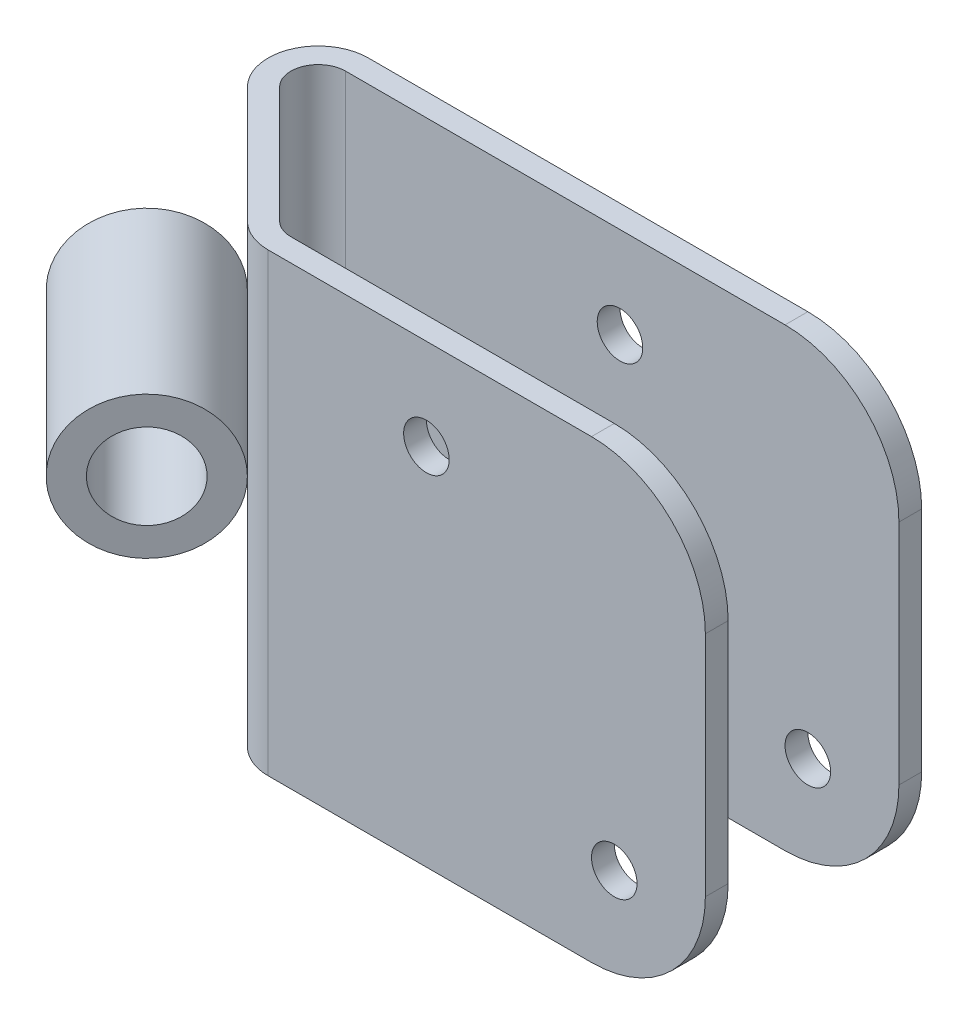
SolidWorks part; units mm, degrees
ref_plane "Front Plane" through (0, 0, 0) normal (0, 0, 1) x (1, 0, 0)
ref_plane "Top Plane" through (0, 0, 0) normal (0, 1, 0) x (1, 0, 0)
ref_plane "Right Plane" through (0, 0, 0) normal (1, 0, 0) x (0, 0, -1)
sketch "Sketch1" plane through (0, 0, 0) normal (0, 1, 0) x (1, 0, 0)
  line L0 (46.2173, -24.4543) -> (48.0056, -0.3907) construction
  line L1 (0, 0) -> (61.722, 0)
  line L2 (-3.9513, -9.5393) -> (9.0027, -22.4933)
  line L3 (12.954, -24.13) -> (61.722, -24.13)
  line L4 (61.722, -24.13) -> (61.722, 0) construction
  line L5 (-3.9513, -1.6367) -> (-7.9026, -5.588) construction
  line L6 (-7.9026, -5.588) -> (-9.6987, -3.7919) construction
  arc A0 (0, 0) -> (-3.9513, -9.5393) centre (0, -5.588) ccw
  arc A1 (9.0027, -22.4933) -> (12.954, -24.13) centre (12.954, -18.542) ccw
  dimension "D3" = 5.588
  dimension "D4" = 5.588
  dimension "D6" = 67.31
  dimension "D1" = 24.13
  dimension "D2" = 45
  dimension "D5" = 24.13
  dimension "D7" = 2.54
extrude "Extrude-Thin1" add sketch "Sketch1" along normal mid plane 50.8 thin
ref_plane "Plane5" through (-9.6987, 0, 3.7919) normal (-0.7071, 0, -0.7071) x (-0.7071, 0, 0.7071)
sketch "Sketch2" plane through (-9.6987, 25.4, 3.7919) normal (0.7071, 0, 0.7071) x (0.7071, 0, -0.7071)
  line L0 (0, 0) -> (0, -50.8) construction
  line L1 (0, 0) -> (0, -50.8) construction
  circle A0 centre (-7.9375, -25.4) radius 7.9375
  circle A1 centre (-7.9375, -25.4) radius 4.7625
  point P4 (-11.1421, -22.5042)
  point P6 (0, 0)
  point P7 (0, -25.4)
  dimension "D1" = 15.875
  dimension "D2" = 9.525
extrude "Boss-Extrude2" add sketch "Sketch2" along normal blind 25.4 separate body
fillet "Fillet1" radius 12.7 4 edges at (61.722, -25.4, 22.86) (61.722, -25.4, 1.27) (61.722, 25.4, 1.27) (61.722, 25.4, 22.86)
sketch "Sketch4" plane through (0, 0, 0) normal (0, 0, -1) x (-1, 0, 0)
  line L0 (-51.562, -15.24) -> (-30.607, 15.24) construction
  line L1 (-61.722, 12.7) -> (-61.722, -12.7) construction
  line L2 (-49.022, 25.4) -> (0, 25.4) construction
  line L4 (-49.022, -25.4) -> (0, -25.4) construction
  circle A2 centre (-51.562, -15.24) radius 2.54
  circle A3 centre (-30.607, 15.24) radius 2.54
  point P2 (-50.8054, -13.4423)
  point P7 (-51.562, -12.7117)
  point P8 (-28.522, 14.4423)
  point P9 (-51.562, -10.5199)
  point P10 (-44.5137, 17.78)
  point P16 (-44.6804, -25.4)
  dimension "D3" = 10.16
  dimension "D1" = 5.08
  dimension "D2" = 31.115
  dimension "D4" = 10.16
  dimension "D5.4" = 10.16
extrude "Cut-Extrude1" cut sketch "Sketch4" against normal through all
